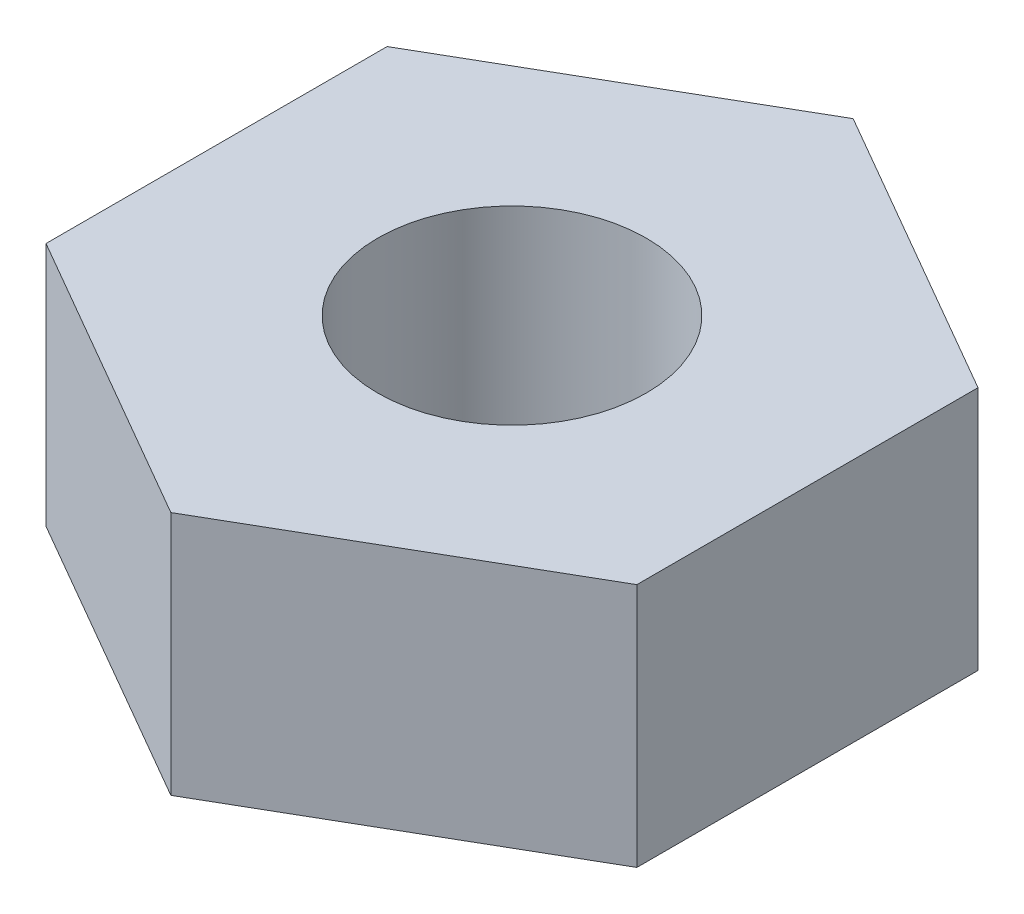
SolidWorks part; units mm, degrees
ref_plane "Front Plane" through (0, 0, 0) normal (0, 0, 1) x (1, 0, 0)
ref_plane "Top Plane" through (0, 0, 0) normal (0, 1, 0) x (1, 0, 0)
ref_plane "Right Plane" through (0, 0, 0) normal (1, 0, 0) x (0, 0, -1)
sketch "Sketch1" plane through (0, 0, 0) normal (0, 1, 0) x (1, 0, 0)
  line L1 (0, -3.1754) -> (2.75, -1.5877)
  line L2 (2.75, -1.5877) -> (2.75, 1.5877)
  line L3 (2.75, 1.5877) -> (0, 3.1754)
  line L4 (0, 3.1754) -> (-2.75, 1.5877)
  line L5 (-2.75, 1.5877) -> (-2.75, -1.5877)
  line L6 (-2.75, -1.5877) -> (0, -3.1754)
  circle A0 centre (0, 0) radius 2.75 construction
  circle A1 centre (0, 0) radius 1.25
  dimension "D1" = 2.5
  dimension "D2" = 5.5
extrude "Boss-Extrude1" add sketch "Sketch1" along normal blind 2.28
